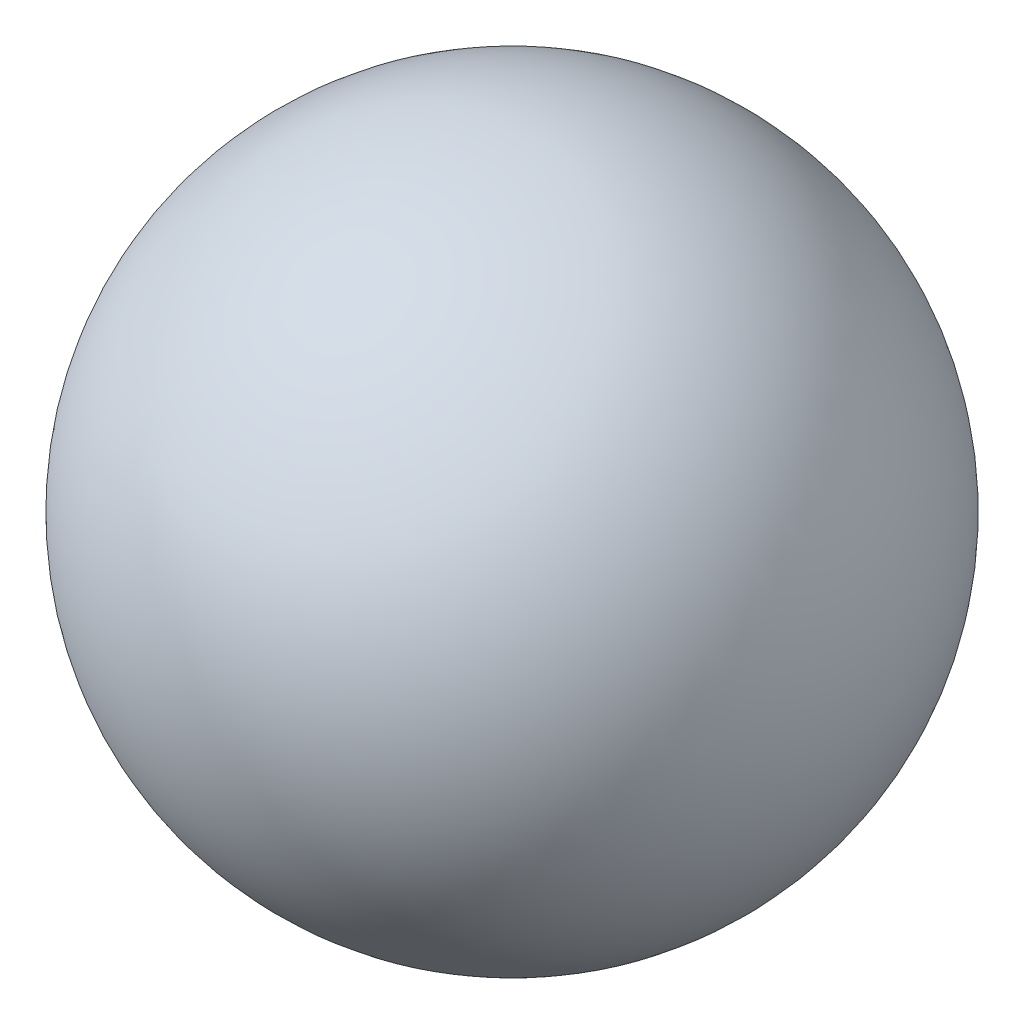
SolidWorks part; units mm, degrees
material "AISI 1015 Steel, Cold Drawn (SS)"
ref_plane "Front Plane" through (0, 0, 0) normal (0, 0, 1) x (1, 0, 0)
ref_plane "Top Plane" through (0, 0, 0) normal (0, 1, 0) x (1, 0, 0)
ref_plane "Right Plane" through (0, 0, 0) normal (1, 0, 0) x (0, 0, -1)
sketch "Sketch1" plane through (0, 0, 0) normal (0, 0, 1) x (1, 0, 0)
  line L0 (0, 0.889) -> (0, -0.889)
  arc A0 (0, 0.889) -> (0, -0.889) centre (0, 0) ccw
  dimension "D1" = 1.778
revolve "Revolve1" add sketch "Sketch1" angle 360 about L0
